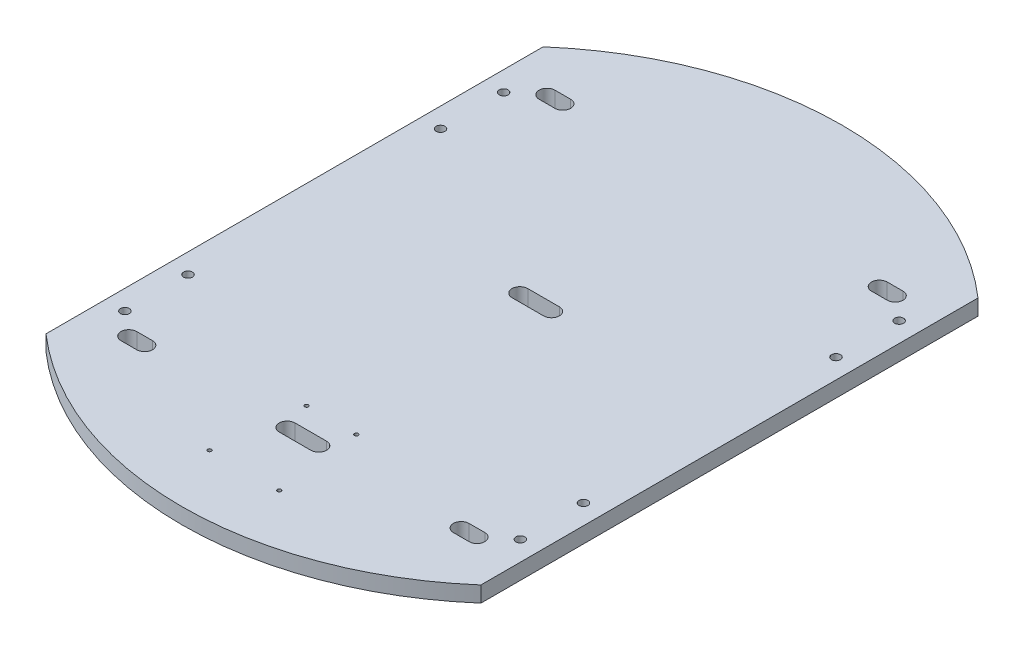
SolidWorks part; units mm, degrees
ref_plane "Front Plane" through (0, 0, 0) normal (0, 0, 1) x (1, 0, 0)
ref_plane "Top Plane" through (0, 0, 0) normal (0, 1, 0) x (1, 0, 0)
ref_plane "Right Plane" through (0, 0, 0) normal (1, 0, 0) x (0, 0, -1)
sketch "Sketch1" plane through (0, 0, 0) normal (0, 1, 0) x (1, 0, 0)
  line L0 (-12.7, -168.25) -> (12.7, -168.25) construction
  line L7 (175, -200) -> (-175, -200) construction
  line L16 (175, -200) -> (175, 200)
  line L21 (175, 200) -> (-175, 200) construction
  line L22 (-175, -200) -> (-175, 200)
  line L23 (175, -200) -> (-175, 200) construction
  line L24 (175, 200) -> (-175, -200) construction
  line L25 (175, -12.7) -> (-175, -12.7) construction
  line L26 (175, -12.7) -> (175, 12.7) construction
  line L28 (-175, -12.7) -> (-175, 12.7) construction
  line L29 (175, -12.7) -> (-175, 12.7) construction
  line L30 (175, 12.7) -> (-175, -12.7) construction
  line L31 (-12.7, -161.9) -> (12.7, -161.9)
  line L32 (-12.7, -174.6) -> (12.7, -174.6)
  line L60 (20, -145.3) -> (28, -215.3) construction
  line L61 (28, -215.3) -> (-28, -215.3) construction
  line L62 (-28, -215.3) -> (-20, -145.3) construction
  line L63 (-20, -145.3) -> (20, -145.3) construction
  line L64 (0, -215.3) -> (0, -145.3) construction
  line L65 (-140.07, -168.25) -> (-127.37, -168.25) construction
  line L66 (-140.07, -161.9) -> (-127.37, -161.9)
  line L67 (-140.07, -174.6) -> (-127.37, -174.6)
  line L68 (127.37, -168.25) -> (140.07, -168.25) construction
  line L69 (127.37, -161.9) -> (140.07, -161.9)
  line L70 (127.37, -174.6) -> (140.07, -174.6)
  line L71 (-140.07, 168.25) -> (-127.37, 168.25) construction
  line L72 (-140.07, 174.6) -> (-127.37, 174.6)
  line L73 (-140.07, 161.9) -> (-127.37, 161.9)
  line L74 (127.37, 168.25) -> (140.07, 168.25) construction
  line L75 (127.37, 174.6) -> (140.07, 174.6)
  line L76 (127.37, 161.9) -> (140.07, 161.9)
  line L77 (-133.72, 168.25) -> (133.72, -168.25) construction
  line L78 (-133.72, 168.25) -> (133.72, 168.25) construction
  line L79 (-133.72, 168.25) -> (-133.72, -168.25) construction
  line L80 (-133.72, -168.25) -> (133.72, -168.25) construction
  line L81 (133.72, 168.25) -> (133.72, -168.25) construction
  line L82 (-133.72, -168.25) -> (133.72, 168.25) construction
  line L83 (175, 12.7) -> (-175, 12.7) construction
  line L84 (-12.7, 19.05) -> (12.7, 19.05) construction
  line L85 (-12.7, 25.4) -> (12.7, 25.4)
  line L86 (-12.7, 12.7) -> (12.7, 12.7)
  line L87 (-175, 0) -> (175, 0) construction
  line L88 (0, 0) -> (0, -200) construction
  arc A5 (-175, -200) -> (175, -200) centre (0, 0) ccw
  arc A6 (-175, 200) -> (-175, -200) centre (0, 0) ccw construction
  arc A8 (175, -200) -> (175, 200) centre (0, 0) ccw construction
  arc A9 (175, 200) -> (-175, 200) centre (0, 0) ccw
  arc A10 (-12.7, -161.9) -> (-12.7, -174.6) centre (-12.7, -168.25) ccw
  arc A11 (12.7, -174.6) -> (12.7, -161.9) centre (12.7, -168.25) ccw
  circle A19 centre (20, -145.3) radius 1.5
  circle A20 centre (-20, -145.3) radius 1.5
  circle A21 centre (28, -215.3) radius 1.5
  circle A22 centre (-28, -215.3) radius 1.5
  arc A23 (-140.07, -161.9) -> (-140.07, -174.6) centre (-140.07, -168.25) ccw
  arc A24 (-127.37, -174.6) -> (-127.37, -161.9) centre (-127.37, -168.25) ccw
  arc A25 (127.37, -161.9) -> (127.37, -174.6) centre (127.37, -168.25) ccw
  arc A26 (140.07, -174.6) -> (140.07, -161.9) centre (140.07, -168.25) ccw
  arc A27 (-140.07, 174.6) -> (-140.07, 161.9) centre (-140.07, 168.25) ccw
  arc A28 (-127.37, 161.9) -> (-127.37, 174.6) centre (-127.37, 168.25) ccw
  arc A29 (127.37, 174.6) -> (127.37, 161.9) centre (127.37, 168.25) ccw
  arc A30 (140.07, 161.9) -> (140.07, 174.6) centre (140.07, 168.25) ccw
  arc A31 (-12.7, 25.4) -> (-12.7, 12.7) centre (-12.7, 19.05) ccw
  arc A32 (12.7, 12.7) -> (12.7, 25.4) centre (12.7, 19.05) ccw
  circle A33 centre (-159.12, -101.6) radius 3.5687
  circle A34 centre (-159.12, -152.4) radius 3.5687
  circle A35 centre (-159.12, 152.4) radius 3.5687
  circle A36 centre (-159.12, 101.6) radius 3.5687
  circle A37 centre (159.12, -152.4) radius 3.5687
  circle A38 centre (159.12, -101.6) radius 3.5687
  circle A39 centre (159.12, 101.6) radius 3.5687
  circle A40 centre (159.12, 152.4) radius 3.5687
  point P11 (0, -168.25)
  point P29 (-133.72, -168.25)
  point P36 (133.72, -168.25)
  point P43 (-133.72, 168.25)
  point P50 (133.72, 168.25)
  point P60 (0, 0)
  point P62 (0, 19.05)
  dimension "D6" = 40
  dimension "D7" = 56
  dimension "D8" = 70
  dimension "D9" = 16.6
  dimension "D10" = 12.7
  dimension "D11" = 12.7
  dimension "D12" = 6.35
  dimension "D13" = 267.44
  dimension "D4" = 3
  dimension "D17" = 7.1374
  dimension "D1" = 350
  dimension "D2" = 400
  dimension "D3" = 25.4
  dimension "D5" = 25.4
  dimension "D14" = 336.5
  dimension "D15" = 50.8
  dimension "D16" = 101.6
  dimension "D18" = 15.88
extrude "Boss-Extrude1" add sketch "Sketch1" along normal blind 12.7
